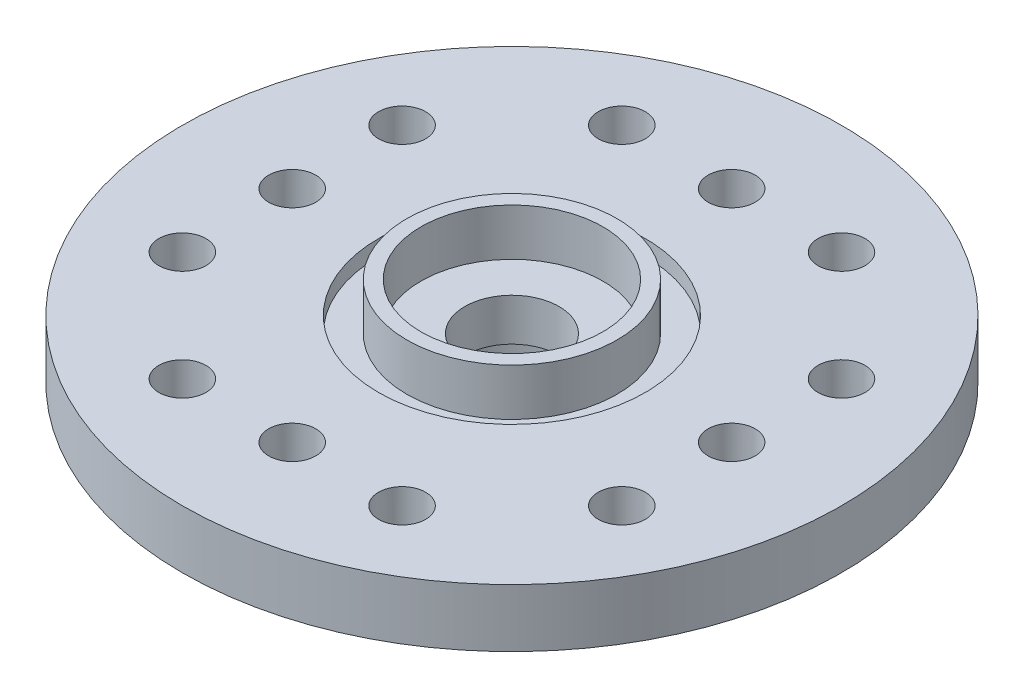
SolidWorks part; units mm, degrees
ref_plane "Front Plane" through (0, 0, 0) normal (0, 0, 1) x (1, 0, 0)
ref_plane "Top Plane" through (0, 0, 0) normal (0, 1, 0) x (1, 0, 0)
ref_plane "Right Plane" through (0, 0, 0) normal (1, 0, 0) x (0, 0, -1)
sketch "Sketch1" plane through (0, 0, 0) normal (0, 1, 0) x (1, 0, 0)
  circle A0 centre (0, 0) radius 10.5
  dimension "D1" = 21
extrude "Boss-Extrude1" add sketch "Sketch1" along normal blind 1.85
sketch "Sketch2" plane through (0, 1.85, 0) normal (0, 1, 0) x (1, 0, 0)
  circle A0 centre (0, 0) radius 4.25
  dimension "D1" = 8.5
extrude "Cut-Extrude1" cut sketch "Sketch2" against normal blind 0.5
sketch "Sketch3" plane through (0, 1.35, 0) normal (0, 1, 0) x (1, 0, 0)
  circle A0 centre (0, 0) radius 3.35
  circle A1 centre (0, 0) radius 2.9
  dimension "D1" = 6.7
  dimension "D2" = 5.8
extrude "Boss-Extrude2" add sketch "Sketch3" along normal blind 1.5
sketch "Sketch4" plane through (0, 0, 0) normal (0, -1, 0) x (1, 0, 0)
  circle A0 centre (0, 0) radius 4.5
  circle A1 centre (0, 0) radius 2.75
  dimension "D1" = 9
  dimension "D2" = 5.5
extrude "Boss-Extrude3" add sketch "Sketch4" along normal blind 3.5
sketch "Sketch5" plane through (0, 1.35, 0) normal (0, 1, 0) x (1, 0, 0)
  circle A0 centre (0, 0) radius 1.5
  dimension "D1" = 3
extrude "Cut-Extrude2" cut sketch "Sketch5" against normal through all
sketch "Sketch6" plane through (0, 1.85, 0) normal (0, 1, 0) x (1, 0, 0)
  line L0 (-3.5, 7) -> (0, 7) construction
  line L1 (0, 7) -> (3.5, 7) construction
  line L2 (0, 7) -> (0, 0) construction
  circle A0 centre (-3.5, 7) radius 0.75
  circle A1 centre (0, 7) radius 0.75
  circle A2 centre (3.5, 7) radius 0.75
  dimension "D2" = 1.5
  dimension "D3" = 7
  dimension "D1" = 7
extrude "Cut-Extrude3" cut sketch "Sketch6" against normal through all
pattern_circular "CirPattern1" count 4 over 360 about axis through (0, 0, 0) along (0, 1, 0) of "Cut-Extrude3"
